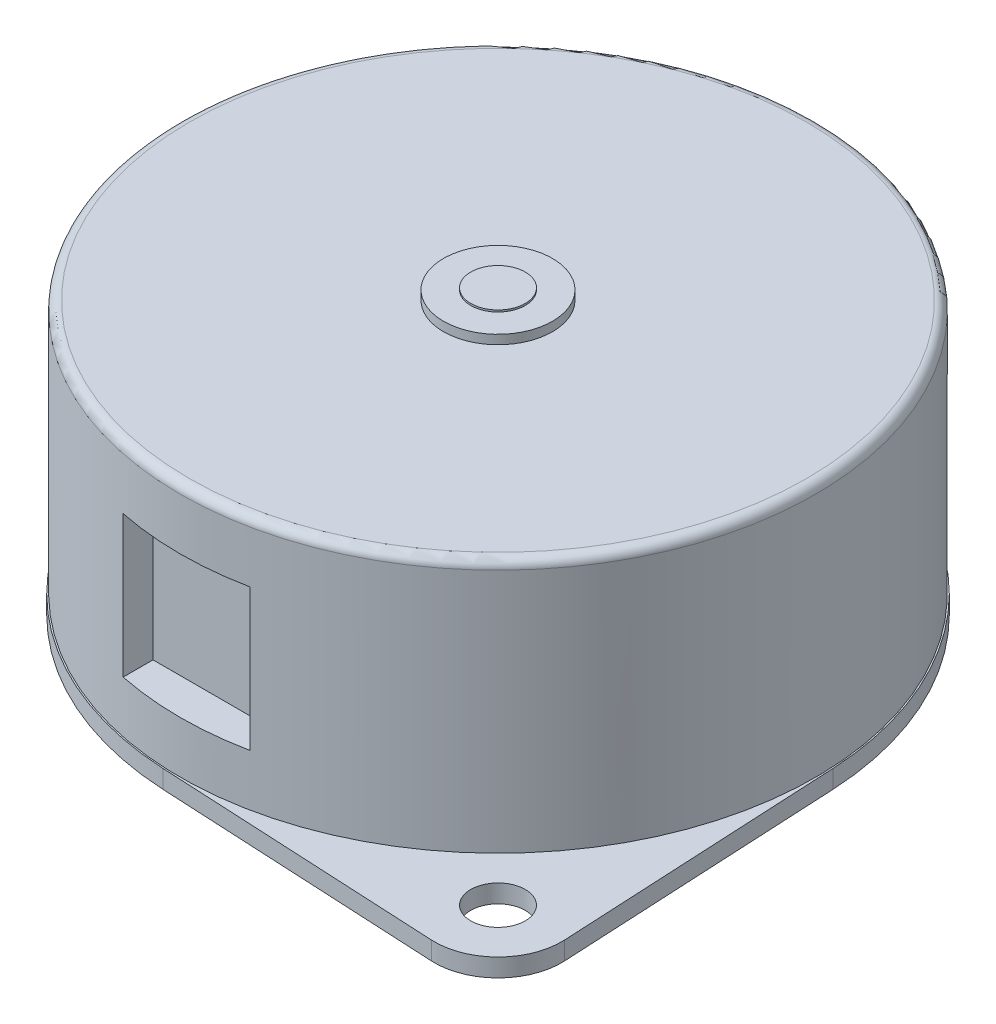
SolidWorks part; units mm, degrees
ref_plane "Front Plane" through (0, 0, 0) normal (0, 0, 1) x (1, 0, 0)
ref_plane "Top Plane" through (0, 0, 0) normal (0, 1, 0) x (1, 0, 0)
ref_plane "Right Plane" through (0, 0, 0) normal (1, 0, 0) x (0, 0, -1)
sketch "Sketch1" plane through (0, 0, 0) normal (0, 1, 0) x (1, 0, 0)
  circle A0 centre (0, 0) radius 17.5
  dimension "D1" = 35
extrude "Boss-Extrude1" add sketch "Sketch1" along normal blind 14
sketch "Sketch2" plane through (0, 0, 0) normal (0, -1, 0) x (1, 0, 0)
  line L0 (0, 17.5) -> (0, -17.5766) construction
  line L1 (-12.4285, -12.4285) -> (12.3744, 12.3744) construction
  line L2 (14.6716, 18.3447) -> (-0.8919, 17.5539)
  line L3 (18.3447, 14.6716) -> (17.5539, -0.8919)
  line L4 (17.3241, 17.3241) -> (18.5936, 18.5936) construction
  line L5 (-18.3447, -14.6716) -> (-17.5539, 0.8919)
  line L6 (-14.6716, -18.3447) -> (0.8919, -17.5539)
  arc A0 (-0.8919, 17.5539) -> (-17.5539, 0.8919) centre (0, 0) ccw
  arc A1 (18.3447, 14.6716) -> (14.6716, 18.3447) centre (14.8492, 14.8492) ccw
  arc A2 (-18.3447, -14.6716) -> (-14.6716, -18.3447) centre (-14.8492, -14.8492) ccw
  circle A3 centre (14.8492, 14.8492) radius 1.5
  circle A4 centre (-14.8492, -14.8492) radius 1.5
  arc A5 (0.8919, -17.5539) -> (17.5539, -0.8919) centre (0, 0) ccw
  circle A6 centre (0, 0) radius 17.5766 construction
  point P7 (14.8492, 14.8492)
  point P8 (-14.8492, -14.8492)
  dimension "D4" = 7
  dimension "D5" = 3
  dimension "D6" = 3
  dimension "D1" = 45
  dimension "D2" = 42
  dimension "D3" = 21
extrude "Boss-Extrude2" add sketch "Sketch2" along normal blind 1
sketch "Sketch3" plane through (0, -1, 0) normal (0, -1, 0) x (1, 0, 0)
  circle A0 centre (0, 0) radius 5
  dimension "D1" = 10
extrude "Boss-Extrude3" add sketch "Sketch3" along normal blind 1.5
sketch "Sketch4" plane through (0, -2.5, 0) normal (0, -1, 0) x (1, 0, 0)
  circle A0 centre (0, 0) radius 1.5
  dimension "D1" = 3
extrude "Boss-Extrude4" add sketch "Sketch4" along normal blind 11
sketch "Sketch5" plane through (0, 14, 0) normal (0, 1, 0) x (1, 0, 0)
  circle A0 centre (0, 0) radius 3
  dimension "D1" = 6
extrude "Boss-Extrude5" add sketch "Sketch5" along normal blind 0.5
sketch "Sketch6" plane through (0, 14.5, 0) normal (0, 1, 0) x (1, 0, 0)
  circle A0 centre (0, 0) radius 1.5
extrude "Boss-Extrude6" add sketch "Sketch6" along normal blind 0.1
fillet "Fillet1" radius 0.5 1 edges at (0, 14, 17.5)
ref_plane "Plane1" through (0, 0, 17.5) normal (0, 0, 1) x (1, 0, 0)
sketch "Sketch7" plane through (0, 0, 17.5) normal (0, 0, 1) x (1, 0, 0)
  line L0 (0, 0) -> (0, 17.2276) construction
  line L1 (-3.5, 10.65) -> (3.5, 10.65)
  line L2 (-3.5, 10.65) -> (-3.5, 2.85)
  line L3 (-3.5, 2.85) -> (3.5, 2.85)
  line L4 (3.5, 10.65) -> (3.5, 2.85)
  line L5 (17.5, 6.75) -> (-17.5, 6.75) construction
  line L6 (17.5, 0) -> (17.5, 13.5) construction
  line L7 (-17.5, 13.5) -> (-17.5, 0) construction
  point P13 (0, 10.65)
  point P14 (-3.5, 6.75)
  dimension "D1" = 7.8
  dimension "D2" = 7
extrude "Cut-Extrude3" cut sketch "Sketch7" against normal blind 2
